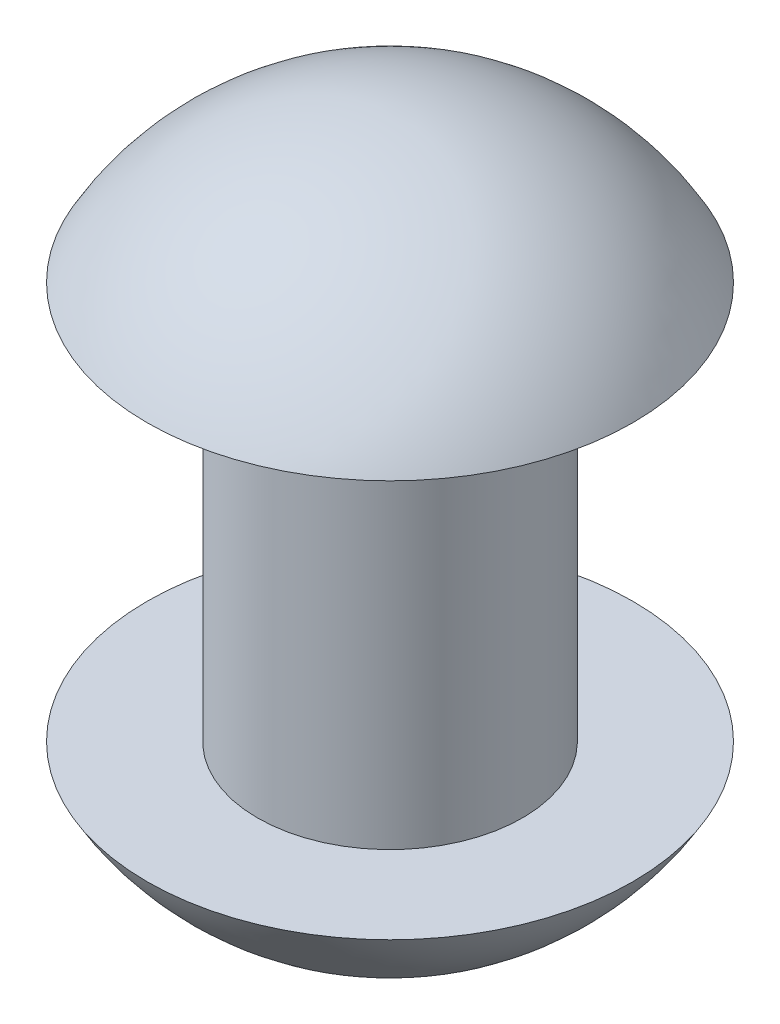
SolidWorks part; units mm, degrees
ref_plane "Ebene vorne" through (0, 0, 0) normal (0, 0, 1) x (1, 0, 0)
ref_plane "Ebene oben" through (0, 0, 0) normal (0, 1, 0) x (1, 0, 0)
ref_plane "Ebene rechts" through (0, 0, 0) normal (1, 0, 0) x (0, 0, -1)
sketch "Sketch1" plane through (0, 0, 0) normal (0, 0, 1) x (1, 0, 0)
  line L0 (-0.12, 0) -> (-0.12, 0.36)
  line L1 (-0.12, 0.36) -> (-0.22, 0.36)
  line L3 (0, 0.3701) -> (0, 0.18) construction
  line L4 (-0.12, 0) -> (-0.22, 0)
  line L8 (0, 0.4889) -> (0, -0.1289)
  line L9 (0, 0.18) -> (-0.3429, 0.18) construction
  arc A0 (-0.22, 0.36) -> (0, 0.4889) centre (0, 0.2368) cw
  arc A2 (-0.22, 0) -> (0, -0.1289) centre (0, 0.1232) ccw
  point P6 (0, 0.4889)
  point P10 (-0.12, 0.18)
  point P14 (0.1706, -0.077)
  dimension "D1" = 0.12
  dimension "D2" = 0.1
  dimension "D3" = 0.36
revolve "Revolve1" add sketch "Sketch1" angle 360 about L8
